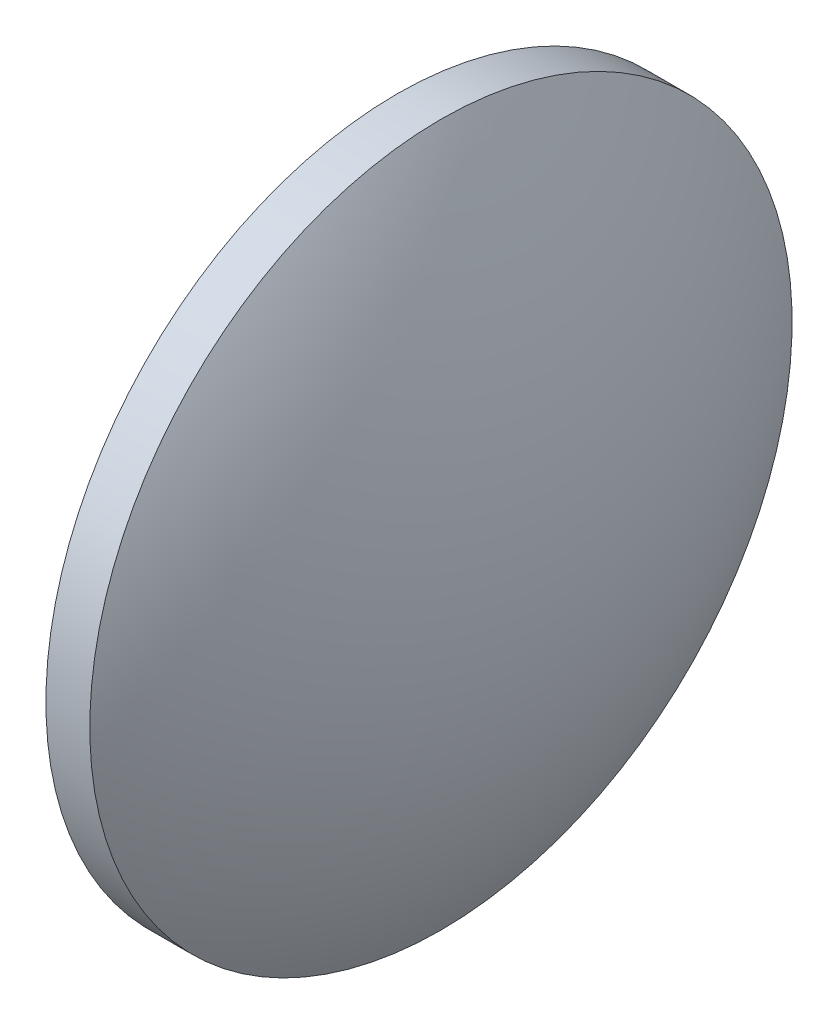
SolidWorks part; units mm, degrees
ref_plane "前视基准面" through (0, 0, 0) normal (0, 0, 1) x (1, 0, 0)
ref_plane "上视基准面" through (0, 0, 0) normal (0, 1, 0) x (1, 0, 0)
ref_plane "右视基准面" through (0, 0, 0) normal (1, 0, 0) x (0, 0, -1)
sketch "草图1" plane through (0, 0, 0) normal (0, 0, 1) x (1, 0, 0)
  line L0 (134.9046, 96.5608) -> (137.4046, 96.5608)
  line L1 (137.4046, 96.5608) -> (137.4046, 56.5608)
  line L2 (137.4046, 56.5608) -> (134.9046, 56.5608)
  line L3 (134.9046, 56.5608) -> (134.9046, 96.5608)
  line L4 (104.1086, 76.5608) -> (168.2007, 76.5608) construction
  arc A0 (134.9046, 96.5608) -> (134.9046, 56.5608) centre (168.2007, 76.5608) ccw
  arc A1 (137.4046, 56.5608) -> (137.4046, 96.5608) centre (104.1086, 76.5608) ccw
  dimension "D1" = 2.5
  dimension "D2" = 40
revolve "旋转1" add sketch "草图1" angle 360 about L4
